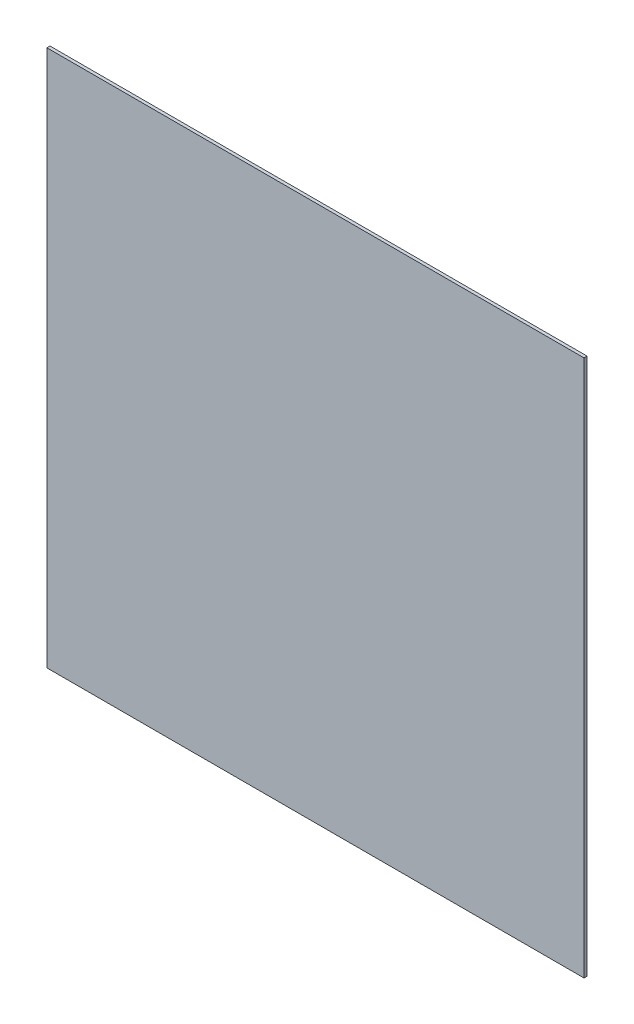
SolidWorks part; units mm, degrees
ref_plane "Front Plane" through (0, 0, 0) normal (0, 0, 1) x (1, 0, 0)
ref_plane "Top Plane" through (0, 0, 0) normal (0, 1, 0) x (1, 0, 0)
ref_plane "Right Plane" through (0, 0, 0) normal (1, 0, 0) x (0, 0, -1)
sketch "Sketch1" plane through (0, 0, 0) normal (0, 0, 1) x (1, 0, 0)
  line L1 (-1830, -1830) -> (1830, -1830)
  line L2 (-1830, -1830) -> (-1830, 1830)
  line L3 (-1830, 1830) -> (1830, 1830)
  line L4 (1830, -1830) -> (1830, 1830)
  line L5 (-1830, -1830) -> (1830, 1830) construction
  line L6 (-1830, 1830) -> (1830, -1830) construction
  point P0 (0, 0)
  dimension "D1" = 3660
  dimension "D2" = 3660
extrude "Boss-Extrude1" add sketch "Sketch1" along normal blind 21 contours L2 L3 L4 L1
